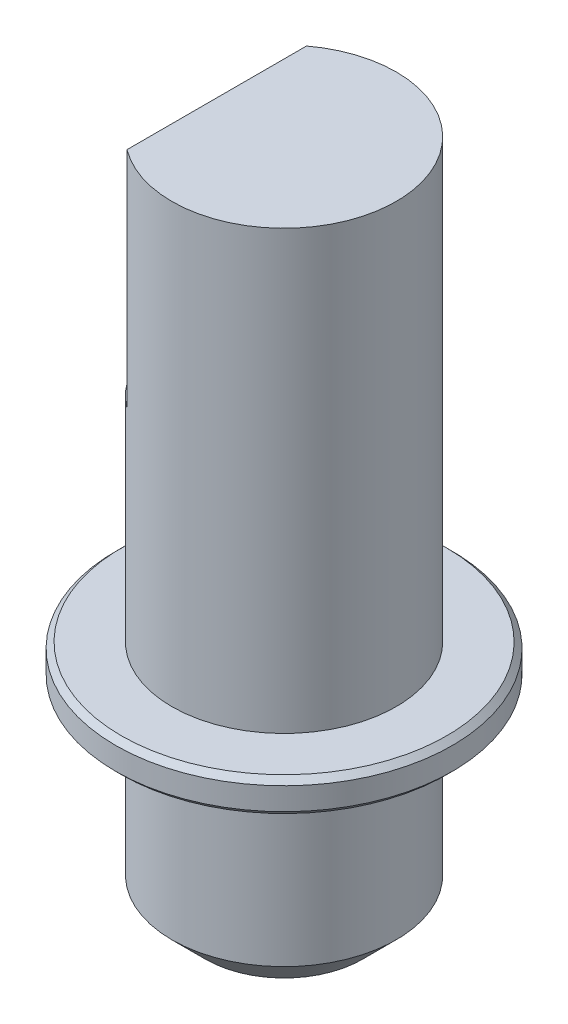
SolidWorks part; units mm, degrees
material "Alloy Steel (SS)"
ref_plane "Front Plane" through (0, 0, 0) normal (0, 0, 1) x (1, 0, 0)
ref_plane "Top Plane" through (0, 0, 0) normal (0, 1, 0) x (1, 0, 0)
ref_plane "Right Plane" through (0, 0, 0) normal (1, 0, 0) x (0, 0, -1)
sketch "Sketch1" plane through (0, 0, 0) normal (0, 1, 0) x (1, 0, 0)
  circle A0 centre (0, 0) radius 10
  dimension "D1" = 20
extrude "Boss-Extrude1" add sketch "Sketch1" along normal blind 60
sketch "Sketch2" plane through (0, 0, 0) normal (0, -1, 0) x (1, 0, 0)
  circle A0 centre (0, 0) radius 4
  dimension "D1" = 8
extrude "Cut-Extrude1" cut sketch "Sketch2" against normal blind 15
sketch "Sketch3" plane through (0, 0, 0) normal (0, -1, 0) x (1, 0, 0)
  line L0 (-2.5, 3.1225) -> (-2.5, -3.1225)
  circle A0 centre (0, 0) radius 4 construction
  arc A1 (-2.5, 3.1225) -> (-2.5, -3.1225) centre (0, 0) ccw
  dimension "D1" = 2.5
extrude "Boss-Extrude2" add sketch "Sketch3" against normal up to next
sketch "Sketch4" plane through (0, 60, 0) normal (0, 1, 0) x (1, 0, 0)
  line L0 (-6, 8) -> (-6, -8)
  circle A0 centre (0, 0) radius 10 construction
  arc A1 (-6, 8) -> (-6, -8) centre (0, 0) ccw
  dimension "D1" = 6
extrude "Cut-Extrude2" cut sketch "Sketch4" against normal blind 20
chamfer "Chamfer3" distance 3 angle 45 1 edges at (0, 0, 10)
sketch "Sketch5" plane through (0, 0, 0) normal (0, 1, 0) x (1, 0, 0)
  circle A0 centre (0, 0) radius 15
  dimension "D1" = 30
extrude "Boss-Extrude3" add sketch "Sketch5" along normal blind 3 from offset 18
chamfer "Chamfer4" distance 0.5 angle 45 2 edges at (0, 18, 15) (0, 21, 15)
